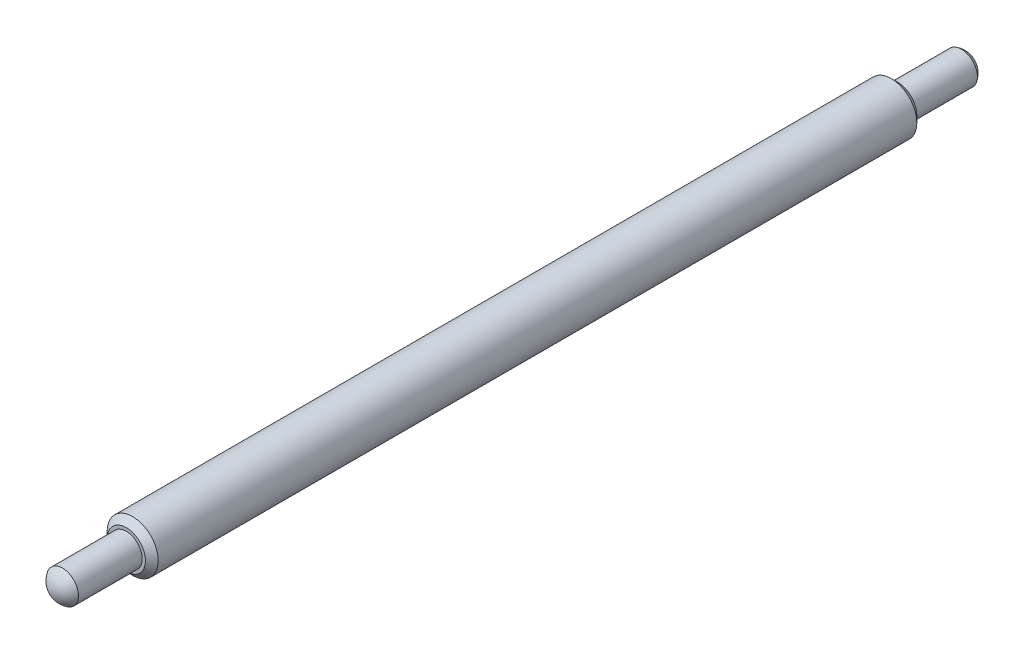
SolidWorks part; units mm, degrees
ref_plane "Front Plane" through (0, 0, 0) normal (0, 0, 1) x (1, 0, 0)
ref_plane "Top Plane" through (0, 0, 0) normal (0, 1, 0) x (1, 0, 0)
ref_plane "Right Plane" through (0, 0, 0) normal (1, 0, 0) x (0, 0, -1)
sketch "Sketch2" plane through (0, 0, 0) normal (1, 0, 0) x (0, 0, -1)
  line L0 (65.5, 0) -> (-5, 0)
  line L1 (-5, 0) -> (-5.7, 0)
  line L3 (65.5, 0) -> (66.2, 0)
  line L5 (65.5, -1.25) -> (60.5, -1.25)
  line L6 (60.5, -1.25) -> (60.5, -2)
  line L7 (60.5, -2) -> (0, -2)
  line L8 (0, -2) -> (0, -1.25)
  line L9 (0, -1.25) -> (-5, -1.25)
  arc A0 (65.5, -1.25) -> (66.2, 0) centre (64.7339, 0) ccw
  arc A1 (-5.7, 0) -> (-5, -1.25) centre (-4.2339, 0) ccw
  dimension "D1" = 0.7
revolve "Revolve1" add sketch "Sketch2" angle 360 about L0
chamfer "Chamfer1" distance 0.5 angle 45 2 edges at (-2, 0, -60.5) (-2, 0, 0)
